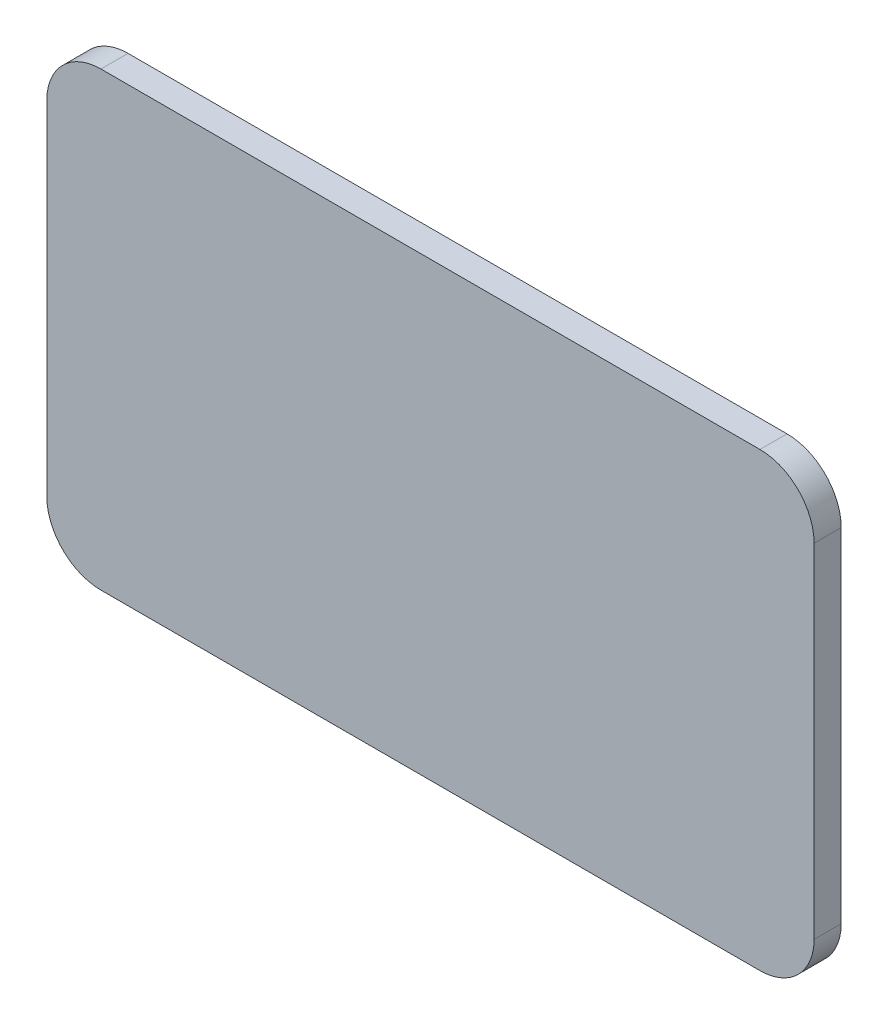
SolidWorks part; units mm, degrees
ref_plane "Front Plane" through (0, 0, 0) normal (0, 0, 1) x (1, 0, 0)
ref_plane "Top Plane" through (0, 0, 0) normal (0, 1, 0) x (1, 0, 0)
ref_plane "Right Plane" through (0, 0, 0) normal (1, 0, 0) x (0, 0, -1)
sketch "Sketch1" plane through (0, 0, 0) normal (0, 0, 1) x (1, 0, 0)
  line L0 (0, 0) -> (16108.8022, 0) construction
  line L1 (-36.5, -25) -> (36.5, -25)
  line L2 (-42.5, -19) -> (-42.5, 19)
  line L3 (-36.5, 25) -> (36.5, 25)
  line L4 (42.5, -19) -> (42.5, 19)
  line L5 (0, 25) -> (0, -16083.8022) construction
  line L6 (24.6393, 6) -> (22.6393, 6)
  line L7 (29.5, 19) -> (24.6393, 19)
  line L8 (29.5, 19) -> (29.5, -19)
  line L9 (29.5, -19) -> (24.6393, -19)
  line L10 (24.6393, 19) -> (24.6393, 6)
  line L11 (24.6393, -6) -> (22.6393, -6)
  line L12 (10.6393, 6) -> (-28.3607, 6)
  line L13 (22.6393, 19) -> (10.6393, 19)
  line L14 (22.6393, 19) -> (22.6393, -19)
  line L15 (22.6393, -19) -> (10.6393, -19)
  line L16 (10.6393, 19) -> (10.6393, 6)
  line L17 (10.6393, -6) -> (-28.3607, -6)
  line L18 (24.6393, -6) -> (24.6393, -19)
  line L19 (10.6393, -6) -> (10.6393, -19)
  line L20 (9.8265, -6.7992) -> (9.8265, -24.187)
  line L21 (9.0135, -6) -> (9.0135, -15.231)
  line L22 (9.0135, -16.044) -> (9.0135, -25)
  line L23 (9.0135, 16.044) -> (9.0135, 25)
  line L24 (9.0135, 6) -> (9.0135, 15.231)
  line L25 (9.8265, 6.7992) -> (9.8265, 24.187)
  line L26 (8.1965, 6.7992) -> (8.1965, 24.187)
  line L27 (7.3835, 16.044) -> (7.3835, 25)
  line L28 (7.3835, 6) -> (7.3835, 15.231)
  line L29 (6.5665, 6.7992) -> (6.5665, 24.187)
  line L30 (5.7535, 16.044) -> (5.7535, 25)
  line L31 (5.7535, 6) -> (5.7535, 15.231)
  line L32 (4.9365, 6.7992) -> (4.9365, 24.187)
  line L33 (4.1235, 16.044) -> (4.1235, 25)
  line L34 (4.1235, 6) -> (4.1235, 15.231)
  line L35 (3.3065, 6.7992) -> (3.3065, 24.187)
  line L36 (2.4935, 16.044) -> (2.4935, 25)
  line L37 (2.4935, 6) -> (2.4935, 15.231)
  line L38 (1.6765, 6.7992) -> (1.6765, 24.187)
  line L39 (0.8635, 16.044) -> (0.8635, 25)
  line L40 (0.8635, 6) -> (0.8635, 15.231)
  line L41 (0.0465, 6.7992) -> (0.0465, 24.187)
  line L42 (-0.7665, 16.044) -> (-0.7665, 25)
  line L43 (-0.7665, 6) -> (-0.7665, 15.231)
  line L44 (-1.5835, 6.7992) -> (-1.5835, 24.187)
  line L45 (-2.3965, 16.044) -> (-2.3965, 25)
  line L46 (-2.3965, 6) -> (-2.3965, 15.231)
  line L47 (-3.2135, 6.7992) -> (-3.2135, 24.187)
  line L48 (-4.0265, 16.044) -> (-4.0265, 25)
  line L49 (-4.0265, 6) -> (-4.0265, 15.231)
  line L50 (-4.8435, 6.7992) -> (-4.8435, 24.187)
  line L51 (-5.6565, 16.044) -> (-5.6565, 25)
  line L52 (-5.6565, 6) -> (-5.6565, 15.231)
  line L53 (-6.4735, 6.7992) -> (-6.4735, 24.187)
  line L54 (-7.2865, 16.044) -> (-7.2865, 25)
  line L55 (-7.2865, 6) -> (-7.2865, 15.231)
  line L56 (-8.1035, 6.7992) -> (-8.1035, 24.187)
  line L57 (-8.9165, 16.044) -> (-8.9165, 25)
  line L58 (-8.9165, 6) -> (-8.9165, 15.231)
  line L59 (-9.7295, 6.7992) -> (-9.7295, 24.187)
  line L60 (-10.5425, 16.044) -> (-10.5425, 25)
  line L61 (-10.5425, 6) -> (-10.5425, 15.231)
  line L62 (-11.3555, 6.7992) -> (-11.3555, 24.187)
  line L63 (8.2005, -6.7992) -> (8.2005, -24.187)
  line L64 (7.3875, -6) -> (7.3875, -15.231)
  line L65 (7.3875, -16.044) -> (7.3875, -25)
  line L66 (6.5745, -6.7992) -> (6.5745, -24.187)
  line L67 (5.7615, -6) -> (5.7615, -15.231)
  line L68 (5.7615, -16.044) -> (5.7615, -25)
  line L69 (4.9485, -6.7992) -> (4.9485, -24.187)
  line L70 (4.1355, -6) -> (4.1355, -15.231)
  line L71 (-12.1685, 16.044) -> (-12.1685, 25) [skipped]
  line L72 (-12.1685, 6) -> (-12.1685, 15.231) [skipped]
  line L73 (-12.9815, 6.7992) -> (-12.9815, 24.187) [skipped]
  line L74 (-13.7945, 16.044) -> (-13.7945, 25) [skipped]
  line L75 (-13.7945, 6) -> (-13.7945, 15.231) [skipped]
  line L76 (-14.6075, 6.7992) -> (-14.6075, 24.187) [skipped]
  line L77 (-15.4205, 6) -> (-15.4205, 15.231) [skipped]
  line L78 (-15.4205, 16.044) -> (-15.4205, 25) [skipped]
  line L79 (4.1355, -16.044) -> (4.1355, -25)
  line L80 (3.3225, -6.7992) -> (3.3225, -24.187)
  line L81 (2.5095, -6) -> (2.5095, -15.231)
  line L82 (2.5095, -16.044) -> (2.5095, -25)
  line L83 (1.6965, -6.7992) -> (1.6965, -24.187)
  line L84 (0.8835, -6) -> (0.8835, -15.231)
  line L85 (0.8835, -16.044) -> (0.8835, -25)
  line L86 (0.0705, -6.7992) -> (0.0705, -24.187)
  line L87 (-0.7425, -6) -> (-0.7425, -15.231)
  line L88 (-0.7425, -16.044) -> (-0.7425, -25)
  line L89 (-1.5555, -6.7992) -> (-1.5555, -24.187)
  line L90 (-2.3685, -6) -> (-2.3685, -15.231)
  line L91 (-2.3685, -16.044) -> (-2.3685, -25)
  line L92 (-3.1815, -6.7992) -> (-3.1815, -24.187)
  line L93 (-3.9945, -6) -> (-3.9945, -15.231)
  line L94 (-3.9945, -16.044) -> (-3.9945, -25)
  line L95 (-4.8075, -6.7992) -> (-4.8075, -24.187)
  line L96 (-5.6205, -6) -> (-5.6205, -15.231)
  line L97 (-5.6205, -16.044) -> (-5.6205, -25)
  line L98 (-6.4335, -6.7992) -> (-6.4335, -24.187)
  line L99 (-7.2465, -6) -> (-7.2465, -15.231)
  line L100 (-7.2465, -16.044) -> (-7.2465, -25)
  line L101 (-8.0595, -6.7992) -> (-8.0595, -24.187)
  line L102 (-8.8725, -6) -> (-8.8725, -15.231)
  line L103 (-8.8725, -16.044) -> (-8.8725, -25)
  line L104 (-9.6855, -6.7992) -> (-9.6855, -24.187)
  line L105 (-10.4985, -6) -> (-10.4985, -15.231)
  line L106 (-10.4985, -16.044) -> (-10.4985, -25)
  line L107 (-11.3115, -6.7992) -> (-11.3115, -24.187)
  line L108 (-15.6607, 5.5) -> (-15.6607, -5.5)
  line L109 (-16.4703, 6) -> (-16.4703, 0.405)
  line L110 (-12.1245, -6) -> (-12.1245, -15.231) [skipped]
  line L111 (-12.1245, -16.044) -> (-12.1245, -25) [skipped]
  line L112 (-16.4703, -6) -> (-16.4703, -0.405)
  line L113 (-17.2907, 5.5) -> (-17.2907, -5.5)
  line L114 (-18.1003, 6) -> (-18.1003, 0.405)
  line L115 (-18.1003, -6) -> (-18.1003, -0.405)
  line L116 (-18.9207, 5.5) -> (-18.9207, -5.5)
  line L117 (-19.7303, 6) -> (-19.7303, 0.405)
  line L118 (-19.7303, -6) -> (-19.7303, -0.405)
  line L119 (-20.5507, 5.5) -> (-20.5507, -5.5)
  line L120 (-21.3603, 6) -> (-21.3603, 0.405)
  line L121 (-21.3603, -6) -> (-21.3603, -0.405)
  line L122 (-22.1807, 5.5) -> (-22.1807, -5.5)
  line L123 (-22.9903, 6) -> (-22.9903, 0.405)
  line L124 (-22.9903, -6) -> (-22.9903, -0.405)
  line L125 (-23.8107, 5.5) -> (-23.8107, -5.5)
  line L126 (-24.6203, 6) -> (-24.6203, 0.405)
  line L127 (-24.6203, -6) -> (-24.6203, -0.405)
  line L128 (-25.4407, 5.5) -> (-25.4407, -5.5)
  line L129 (-26.2503, 6) -> (-26.2503, 0.405)
  line L130 (-26.2503, -6) -> (-26.2503, -0.405)
  line L131 (-27.0707, 5.5) -> (-27.0707, -5.5)
  line L132 (-27.8803, 6) -> (-27.8803, 0.405)
  line L133 (-27.8803, -6) -> (-27.8803, -0.405)
  line L134 (-28.7007, 5.5) -> (-28.7007, -5.5)
  line L137 (-29.5103, 6) -> (-29.5103, 0.405) [skipped]
  line L138 (-29.5103, -6) -> (-29.5103, -0.405) [skipped]
  arc A0 (36.5, 25) -> (42.5, 19) centre (36.5, 19) cw
  arc A1 (36.5, -25) -> (42.5, -19) centre (36.5, -19) ccw
  arc A2 (-36.5, -25) -> (-42.5, -19) centre (-36.5, -19) cw
  arc A3 (-42.5, 19) -> (-36.5, 25) centre (-36.5, 19) cw
  point P0 (0, 0)
  point P10 (0, 25)
  point P259 (42.5, 25)
  point P266 (42.5, -25)
  point P269 (-42.5, -25)
  dimension "D23" = 6
  dimension "D1" = 85
  dimension "D2" = 50
  dimension "D3" = 13
  dimension "D4" = 12
  dimension "D5" = 2
  dimension "D6" = 38
  dimension "D7" = 12
  dimension "D8" = 12
  dimension "D9" = 39
  dimension "D10" = 0.8128
  dimension "D11" = 0.813
  dimension "D12" = 0.813
  dimension "D13" = 0.813
  dimension "D14" = 12
  dimension "D15" = 5
  dimension "D16" = 21.182
  dimension "D18" = 12.7
  dimension "D19" = 11
  dimension "D20" = 0.8096
  dimension "D21" = 0.81
  dimension "D17" = 14
  dimension "D22" = 9
extrude "Boss-Extrude6" add sketch "Sketch1" along normal blind 3
sketch "Sketch3" plane through (0, 0, 3) normal (0, 0, 1) x (1, 0, 0)
  line L0 (9.0135, -16.044) -> (9.0135, -25) construction
  line L1 (9.0135, -6) -> (9.0135, -15.231) construction
  line L2 (9.8265, -6.7992) -> (9.8265, -24.187) construction
  line L3 (10.6393, 6) -> (-28.3607, 6) construction
  line L4 (-36.5, -25) -> (36.5, -25)
  line L5 (42.5, -19) -> (42.5, 19)
  line L6 (36.5, 25) -> (-36.5, 25)
  line L7 (-42.5, 19) -> (-42.5, -19)
  line L8 (-36.5, -25) -> (36.5, -25)
  line L9 (42.5, -19) -> (42.5, 19)
  line L10 (36.5, 25) -> (-36.5, 25)
  line L11 (-42.5, 19) -> (-42.5, -19)
  line L12 (10.6393, 19) -> (10.6393, 6) construction
  line L13 (22.6393, 19) -> (10.6393, 19) construction
  line L14 (22.6393, 19) -> (22.6393, -19) construction
  line L15 (22.6393, -19) -> (10.6393, -19) construction
  line L16 (10.6393, -6) -> (10.6393, -19) construction
  line L17 (10.6393, -6) -> (-28.3607, -6) construction
  line L18 (24.6393, -6) -> (22.6393, -6) construction
  line L19 (24.6393, -6) -> (24.6393, -19) construction
  line L20 (29.5, -19) -> (24.6393, -19) construction
  line L21 (29.5, 19) -> (29.5, -19) construction
  line L22 (29.5, 19) -> (24.6393, 19) construction
  line L23 (24.6393, 19) -> (24.6393, 6) construction
  line L24 (24.6393, 6) -> (22.6393, 6) construction
  line L25 (-10.5425, 16.044) -> (-10.5425, 25) construction
  line L26 (5.7535, 16.044) -> (5.7535, 25) construction
  line L27 (7.3835, 6) -> (7.3835, 15.231) construction
  line L28 (7.3835, 16.044) -> (7.3835, 25) construction
  line L29 (8.1965, 6.7992) -> (8.1965, 24.187) construction
  line L30 (9.8265, 6.7992) -> (9.8265, 24.187) construction
  line L31 (9.0135, 6) -> (9.0135, 15.231) construction
  line L32 (9.0135, 16.044) -> (9.0135, 25) construction
  line L33 (2.4935, 6) -> (2.4935, 15.231) construction
  line L34 (2.4935, 16.044) -> (2.4935, 25) construction
  line L35 (3.3065, 6.7992) -> (3.3065, 24.187) construction
  line L36 (4.1235, 6) -> (4.1235, 15.231) construction
  line L37 (4.1235, 16.044) -> (4.1235, 25) construction
  line L38 (4.9365, 6.7992) -> (4.9365, 24.187) construction
  line L39 (5.7535, 6) -> (5.7535, 15.231) construction
  line L40 (6.5665, 6.7992) -> (6.5665, 24.187) construction
  line L41 (-2.3965, 6) -> (-2.3965, 15.231) construction
  line L42 (-2.3965, 16.044) -> (-2.3965, 25) construction
  line L43 (-0.7665, 6) -> (-0.7665, 15.231) construction
  line L44 (-0.7665, 16.044) -> (-0.7665, 25) construction
  line L45 (0.0465, 6.7992) -> (0.0465, 24.187) construction
  line L46 (0.8635, 6) -> (0.8635, 15.231) construction
  line L47 (0.8635, 16.044) -> (0.8635, 25) construction
  line L48 (1.6765, 6.7992) -> (1.6765, 24.187) construction
  line L49 (-7.2865, 16.044) -> (-7.2865, 25) construction
  line L50 (-5.6565, 6) -> (-5.6565, 15.231) construction
  line L51 (-5.6565, 16.044) -> (-5.6565, 25) construction
  line L52 (-4.8435, 6.7992) -> (-4.8435, 24.187) construction
  line L53 (-4.0265, 6) -> (-4.0265, 15.231) construction
  line L54 (-4.0265, 16.044) -> (-4.0265, 25) construction
  line L55 (-3.2135, 6.7992) -> (-3.2135, 24.187) construction
  line L56 (-1.5835, 6.7992) -> (-1.5835, 24.187) construction
  line L57 (-15.6607, 5.5) -> (-15.6607, -5.5) construction
  line L58 (-10.5425, 6) -> (-10.5425, 15.231) construction
  line L59 (-9.7295, 6.7992) -> (-9.7295, 24.187) construction
  line L60 (-8.9165, 6) -> (-8.9165, 15.231) construction
  line L61 (-8.9165, 16.044) -> (-8.9165, 25) construction
  line L62 (-8.1035, 6.7992) -> (-8.1035, 24.187) construction
  line L63 (-7.2865, 6) -> (-7.2865, 15.231) construction
  line L64 (-6.4735, 6.7992) -> (-6.4735, 24.187) construction
  line L65 (4.9485, -6.7992) -> (4.9485, -24.187) construction
  line L66 (5.7615, -16.044) -> (5.7615, -25) construction
  line L67 (5.7615, -6) -> (5.7615, -15.231) construction
  line L68 (6.5745, -6.7992) -> (6.5745, -24.187) construction
  line L69 (7.3875, -16.044) -> (7.3875, -25) construction
  line L70 (7.3875, -6) -> (7.3875, -15.231) construction
  line L71 (8.2005, -6.7992) -> (8.2005, -24.187) construction
  line L72 (-11.3555, 6.7992) -> (-11.3555, 24.187) construction
  line L73 (4.1355, -6) -> (4.1355, -15.231) construction
  line L74 (0.8835, -16.044) -> (0.8835, -25) construction
  line L75 (0.8835, -6) -> (0.8835, -15.231) construction
  line L76 (1.6965, -6.7992) -> (1.6965, -24.187) construction
  line L77 (2.5095, -16.044) -> (2.5095, -25) construction
  line L78 (2.5095, -6) -> (2.5095, -15.231) construction
  line L79 (3.3225, -6.7992) -> (3.3225, -24.187) construction
  line L80 (4.1355, -16.044) -> (4.1355, -25) construction
  line L81 (-3.9945, -6) -> (-3.9945, -15.231) construction
  line L82 (-3.1815, -6.7992) -> (-3.1815, -24.187) construction
  line L83 (-2.3685, -16.044) -> (-2.3685, -25) construction
  line L84 (-2.3685, -6) -> (-2.3685, -15.231) construction
  line L85 (-1.5555, -6.7992) -> (-1.5555, -24.187) construction
  line L86 (-0.7425, -16.044) -> (-0.7425, -25) construction
  line L87 (-0.7425, -6) -> (-0.7425, -15.231) construction
  line L88 (0.0705, -6.7992) -> (0.0705, -24.187) construction
  line L89 (-8.0595, -6.7992) -> (-8.0595, -24.187) construction
  line L90 (-7.2465, -16.044) -> (-7.2465, -25) construction
  line L91 (-7.2465, -6) -> (-7.2465, -15.231) construction
  line L92 (-6.4335, -6.7992) -> (-6.4335, -24.187) construction
  line L93 (-5.6205, -16.044) -> (-5.6205, -25) construction
  line L94 (-5.6205, -6) -> (-5.6205, -15.231) construction
  line L95 (-4.8075, -6.7992) -> (-4.8075, -24.187) construction
  line L96 (-3.9945, -16.044) -> (-3.9945, -25) construction
  line L97 (-16.4703, -6) -> (-16.4703, -0.405) construction
  line L98 (-16.4703, 6) -> (-16.4703, 0.405) construction
  line L99 (-11.3115, -6.7992) -> (-11.3115, -24.187) construction
  line L100 (-10.4985, -16.044) -> (-10.4985, -25) construction
  line L101 (-10.4985, -6) -> (-10.4985, -15.231) construction
  line L102 (-9.6855, -6.7992) -> (-9.6855, -24.187) construction
  line L103 (-8.8725, -16.044) -> (-8.8725, -25) construction
  line L104 (-8.8725, -6) -> (-8.8725, -15.231) construction
  line L105 (-19.7303, 6) -> (-19.7303, 0.405) construction
  line L106 (-18.9207, 5.5) -> (-18.9207, -5.5) construction
  line L107 (-18.1003, -6) -> (-18.1003, -0.405) construction
  line L108 (-18.1003, 6) -> (-18.1003, 0.405) construction
  line L109 (-17.2907, 5.5) -> (-17.2907, -5.5) construction
  line L110 (-23.8107, 5.5) -> (-23.8107, -5.5) construction
  line L111 (-22.9903, -6) -> (-22.9903, -0.405) construction
  line L112 (-22.9903, 6) -> (-22.9903, 0.405) construction
  line L113 (-22.1807, 5.5) -> (-22.1807, -5.5) construction
  line L114 (-21.3603, -6) -> (-21.3603, -0.405) construction
  line L115 (-21.3603, 6) -> (-21.3603, 0.405) construction
  line L116 (-20.5507, 5.5) -> (-20.5507, -5.5) construction
  line L117 (-19.7303, -6) -> (-19.7303, -0.405) construction
  line L118 (-27.8803, -6) -> (-27.8803, -0.405) construction
  line L119 (-27.8803, 6) -> (-27.8803, 0.405) construction
  line L120 (-27.0707, 5.5) -> (-27.0707, -5.5) construction
  line L121 (-26.2503, -6) -> (-26.2503, -0.405) construction
  line L122 (-26.2503, 6) -> (-26.2503, 0.405) construction
  line L123 (-25.4407, 5.5) -> (-25.4407, -5.5) construction
  line L124 (-24.6203, -6) -> (-24.6203, -0.405) construction
  line L125 (-24.6203, 6) -> (-24.6203, 0.405) construction
  line L126 (-28.7007, 5.5) -> (-28.7007, -5.5) construction
  line L127 (9.0135, -16.044) -> (9.0135, -25)
  line L128 (9.0135, -6) -> (9.0135, -15.231)
  line L129 (9.8265, -6.7992) -> (9.8265, -24.187)
  line L130 (10.6393, 6) -> (-28.3607, 6)
  line L131 (10.6393, 19) -> (10.6393, 6)
  line L132 (22.6393, 19) -> (10.6393, 19)
  line L133 (22.6393, 19) -> (22.6393, -19)
  line L134 (22.6393, -19) -> (10.6393, -19)
  line L135 (10.6393, -6) -> (10.6393, -19)
  line L136 (10.6393, -6) -> (-28.3607, -6)
  line L137 (24.6393, -6) -> (22.6393, -6)
  line L138 (24.6393, -6) -> (24.6393, -19)
  line L139 (29.5, -19) -> (24.6393, -19)
  line L140 (29.5, 19) -> (29.5, -19)
  line L141 (29.5, 19) -> (24.6393, 19)
  line L142 (24.6393, 19) -> (24.6393, 6)
  line L143 (24.6393, 6) -> (22.6393, 6)
  line L144 (-10.5425, 16.044) -> (-10.5425, 25)
  line L145 (5.7535, 16.044) -> (5.7535, 25)
  line L146 (7.3835, 6) -> (7.3835, 15.231)
  line L147 (7.3835, 16.044) -> (7.3835, 25)
  line L148 (8.1965, 6.7992) -> (8.1965, 24.187)
  line L149 (9.8265, 6.7992) -> (9.8265, 24.187)
  line L150 (9.0135, 6) -> (9.0135, 15.231)
  line L151 (9.0135, 16.044) -> (9.0135, 25)
  line L152 (2.4935, 6) -> (2.4935, 15.231)
  line L153 (2.4935, 16.044) -> (2.4935, 25)
  line L154 (3.3065, 6.7992) -> (3.3065, 24.187)
  line L155 (4.1235, 6) -> (4.1235, 15.231)
  line L156 (4.1235, 16.044) -> (4.1235, 25)
  line L157 (4.9365, 6.7992) -> (4.9365, 24.187)
  line L158 (5.7535, 6) -> (5.7535, 15.231)
  line L159 (6.5665, 6.7992) -> (6.5665, 24.187)
  line L160 (-2.3965, 6) -> (-2.3965, 15.231)
  line L161 (-2.3965, 16.044) -> (-2.3965, 25)
  line L162 (-0.7665, 6) -> (-0.7665, 15.231)
  line L163 (-0.7665, 16.044) -> (-0.7665, 25)
  line L164 (0.0465, 6.7992) -> (0.0465, 24.187)
  line L165 (0.8635, 6) -> (0.8635, 15.231)
  line L166 (0.8635, 16.044) -> (0.8635, 25)
  line L167 (1.6765, 6.7992) -> (1.6765, 24.187)
  line L168 (-7.2865, 16.044) -> (-7.2865, 25)
  line L169 (-5.6565, 6) -> (-5.6565, 15.231)
  line L170 (-5.6565, 16.044) -> (-5.6565, 25)
  line L171 (-4.8435, 6.7992) -> (-4.8435, 24.187)
  line L172 (-4.0265, 6) -> (-4.0265, 15.231)
  line L173 (-4.0265, 16.044) -> (-4.0265, 25)
  line L174 (-3.2135, 6.7992) -> (-3.2135, 24.187)
  line L175 (-1.5835, 6.7992) -> (-1.5835, 24.187)
  line L176 (-15.6607, 5.5) -> (-15.6607, -5.5)
  line L177 (-10.5425, 6) -> (-10.5425, 15.231)
  line L178 (-9.7295, 6.7992) -> (-9.7295, 24.187)
  line L179 (-8.9165, 6) -> (-8.9165, 15.231)
  line L180 (-8.9165, 16.044) -> (-8.9165, 25)
  line L181 (-8.1035, 6.7992) -> (-8.1035, 24.187)
  line L182 (-7.2865, 6) -> (-7.2865, 15.231)
  line L183 (-6.4735, 6.7992) -> (-6.4735, 24.187)
  line L184 (4.9485, -6.7992) -> (4.9485, -24.187)
  line L185 (5.7615, -16.044) -> (5.7615, -25)
  line L186 (5.7615, -6) -> (5.7615, -15.231)
  line L187 (6.5745, -6.7992) -> (6.5745, -24.187)
  line L188 (7.3875, -16.044) -> (7.3875, -25)
  line L189 (7.3875, -6) -> (7.3875, -15.231)
  line L190 (8.2005, -6.7992) -> (8.2005, -24.187)
  line L191 (-11.3555, 6.7992) -> (-11.3555, 24.187)
  line L192 (4.1355, -6) -> (4.1355, -15.231)
  line L193 (0.8835, -16.044) -> (0.8835, -25)
  line L194 (0.8835, -6) -> (0.8835, -15.231)
  line L195 (1.6965, -6.7992) -> (1.6965, -24.187)
  line L196 (2.5095, -16.044) -> (2.5095, -25)
  line L197 (2.5095, -6) -> (2.5095, -15.231)
  line L198 (3.3225, -6.7992) -> (3.3225, -24.187)
  line L199 (4.1355, -16.044) -> (4.1355, -25)
  line L200 (-3.9945, -6) -> (-3.9945, -15.231)
  line L201 (-3.1815, -6.7992) -> (-3.1815, -24.187)
  line L202 (-2.3685, -16.044) -> (-2.3685, -25)
  line L203 (-2.3685, -6) -> (-2.3685, -15.231)
  line L204 (-1.5555, -6.7992) -> (-1.5555, -24.187)
  line L205 (-0.7425, -16.044) -> (-0.7425, -25)
  line L206 (-0.7425, -6) -> (-0.7425, -15.231)
  line L207 (0.0705, -6.7992) -> (0.0705, -24.187)
  line L208 (-8.0595, -6.7992) -> (-8.0595, -24.187)
  line L209 (-7.2465, -16.044) -> (-7.2465, -25)
  line L210 (-7.2465, -6) -> (-7.2465, -15.231)
  line L211 (-6.4335, -6.7992) -> (-6.4335, -24.187)
  line L212 (-5.6205, -16.044) -> (-5.6205, -25)
  line L213 (-5.6205, -6) -> (-5.6205, -15.231)
  line L214 (-4.8075, -6.7992) -> (-4.8075, -24.187)
  line L215 (-3.9945, -16.044) -> (-3.9945, -25)
  line L216 (-16.4703, -6) -> (-16.4703, -0.405)
  line L217 (-16.4703, 6) -> (-16.4703, 0.405)
  line L218 (-11.3115, -6.7992) -> (-11.3115, -24.187)
  line L219 (-10.4985, -16.044) -> (-10.4985, -25)
  line L220 (-10.4985, -6) -> (-10.4985, -15.231)
  line L221 (-9.6855, -6.7992) -> (-9.6855, -24.187)
  line L222 (-8.8725, -16.044) -> (-8.8725, -25)
  line L223 (-8.8725, -6) -> (-8.8725, -15.231)
  line L224 (-19.7303, 6) -> (-19.7303, 0.405)
  line L225 (-18.9207, 5.5) -> (-18.9207, -5.5)
  line L226 (-18.1003, -6) -> (-18.1003, -0.405)
  line L227 (-18.1003, 6) -> (-18.1003, 0.405)
  line L228 (-17.2907, 5.5) -> (-17.2907, -5.5)
  line L229 (-23.8107, 5.5) -> (-23.8107, -5.5)
  line L230 (-22.9903, -6) -> (-22.9903, -0.405)
  line L231 (-22.9903, 6) -> (-22.9903, 0.405)
  line L232 (-22.1807, 5.5) -> (-22.1807, -5.5)
  line L233 (-21.3603, -6) -> (-21.3603, -0.405)
  line L234 (-21.3603, 6) -> (-21.3603, 0.405)
  line L235 (-20.5507, 5.5) -> (-20.5507, -5.5)
  line L236 (-19.7303, -6) -> (-19.7303, -0.405)
  line L237 (-27.8803, -6) -> (-27.8803, -0.405)
  line L238 (-27.8803, 6) -> (-27.8803, 0.405)
  line L239 (-27.0707, 5.5) -> (-27.0707, -5.5)
  line L240 (-26.2503, -6) -> (-26.2503, -0.405)
  line L241 (-26.2503, 6) -> (-26.2503, 0.405)
  line L242 (-25.4407, 5.5) -> (-25.4407, -5.5)
  line L243 (-24.6203, -6) -> (-24.6203, -0.405)
  line L244 (-24.6203, 6) -> (-24.6203, 0.405)
  line L245 (-28.7007, 5.5) -> (-28.7007, -5.5)
  arc A4 (36.5, -25) -> (42.5, -19) centre (36.5, -19) ccw
  arc A5 (36.5, -25) -> (42.5, -19) centre (36.5, -19) ccw
  arc A6 (42.5, 19) -> (36.5, 25) centre (36.5, 19) ccw
  arc A7 (42.5, 19) -> (36.5, 25) centre (36.5, 19) ccw
  arc A8 (-36.5, 25) -> (-42.5, 19) centre (-36.5, 19) ccw
  arc A9 (-36.5, 25) -> (-42.5, 19) centre (-36.5, 19) ccw
  arc A10 (-42.5, -19) -> (-36.5, -25) centre (-36.5, -19) ccw
  arc A11 (-42.5, -19) -> (-36.5, -25) centre (-36.5, -19) ccw
  dimension "D1" = 0
